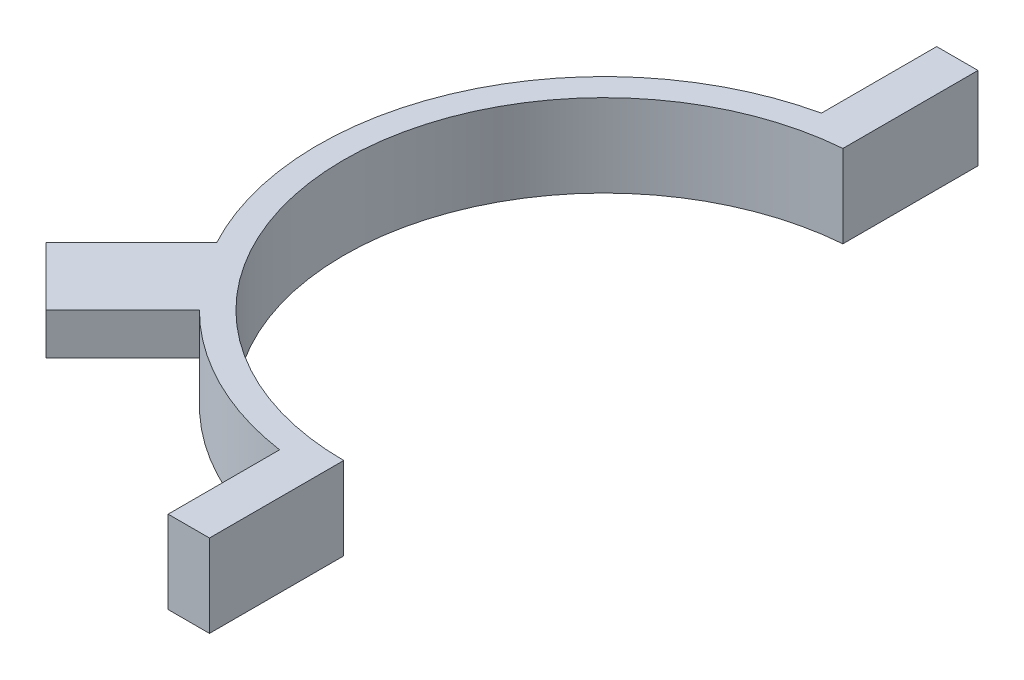
SolidWorks part; units mm, degrees
ref_plane "Front Plane" through (0, 0, 0) normal (0, 0, 1) x (1, 0, 0)
ref_plane "Top Plane" through (0, 0, 0) normal (0, 1, 0) x (1, 0, 0)
ref_plane "Right Plane" through (0, 0, 0) normal (1, 0, 0) x (0, 0, -1)
sketch "Sketch1" plane through (0, 0, 0) normal (0, 1, 0) x (1, 0, 0)
  line L0 (0, -41.9629) -> (0, 37.9148) construction
  line L6 (0, -32.004) -> (0, -35.179)
  line L7 (0, -32.004) -> (0, -35.179) construction
  line L8 (-2.54, 31.903) -> (-2.54, 35.0872)
  arc A0 (-2.54, 31.903) -> (0, -32.004) centre (0, 0) ccw
  arc A1 (-2.54, 35.0872) -> (0, -35.179) centre (0, 0) ccw
  point P4 (0, 0)
  point P8 (-2.54, 35.0872)
  point P9 (-2.54, 31.903)
  point P11 (-2.54, 35.0872)
  point P12 (0, 0)
  dimension "D1" = 64.008
  dimension "D3" = 70.358
  dimension "D4" = 2.54
extrude "Boss-Extrude1" add sketch "Sketch1" along normal blind 10.16
ref_plane "Plane1" through (0, 0, 32.004) normal (0, 0, -1) x (0, -1, 0)
sketch "Sketch3" plane through (0, 0, 32.004) normal (0, 0, -1) x (0, -1, 0)
  line L0 (-10.16, 0) -> (0, 0) construction
  line L1 (-10.16, 5.08) -> (0, 5.08)
  line L2 (-10.16, 5.08) -> (-10.16, 0)
  line L3 (-10.16, 0) -> (0, 0)
  line L4 (0, 5.08) -> (0, 0)
  line L5 (-10.16, 5.08) -> (0, 0) construction
  line L6 (-10.16, 0) -> (0, 5.08) construction
  point P0 (-5.08, 2.54)
  point P7 (0, 0)
  point P9 (0, 0)
  dimension "D1" = 5.08
  dimension "D2" = 10.16
extrude "Boss-Extrude2" add sketch "Sketch3" against normal blind 16.51
ref_plane "Plane2" through (0, 0, -32.004) normal (0, 0, 1) x (0, -1, 0)
sketch "Sketch4" plane through (0, 0, -32.004) normal (0, 0, 1) x (0, -1, 0)
  line L0 (-10.16, -2.54) -> (0, -2.54) construction
  line L1 (-10.16, -2.54) -> (0, -2.54)
  line L2 (-10.16, -2.54) -> (-10.16, -7.62)
  line L3 (-10.16, -7.62) -> (0, -7.62)
  line L4 (0, -2.54) -> (0, -7.62)
  line L5 (-10.16, -2.54) -> (0, -7.62) construction
  line L6 (-10.16, -7.62) -> (0, -2.54) construction
  point P0 (-5.08, -5.08)
  point P7 (0, 0)
  dimension "D1" = 10.16
  dimension "D2" = 5.08
extrude "Boss-Extrude3" add sketch "Sketch4" against normal blind 16.51
sketch "Sketch5" plane through (0, 10.16, 0) normal (0, 1, 0) x (1, 0, 0)
  line L0 (0, 0) -> (0, -54.3839) construction
  line L1 (0, 0) -> (-44.248, -44.248) construction
  line L3 (-22.6302, -22.6302) -> (-34.3046, -34.3046)
  line L4 (-22.6302, -22.6302) -> (-29.8145, -15.446)
  line L5 (-29.8145, -15.446) -> (-41.4888, -27.1204)
  line L6 (-41.4888, -27.1204) -> (-34.3046, -34.3046)
  arc A1 (-2.54, 31.903) -> (0, -32.004) centre (0, 0) ccw construction
  point P2 (0, 0)
  point P8 (0, 0)
  point P15 (-0.1369, -1.0462)
  point P16 (0, 0)
  point P18 (0, 0)
  point P19 (0, 0)
  dimension "D1" = 45
  dimension "D2" = 10.16
  dimension "D3" = 10.16
  dimension "D4" = 16.51
extrude "Boss-Extrude4" add sketch "Sketch5" against normal blind 5.08
